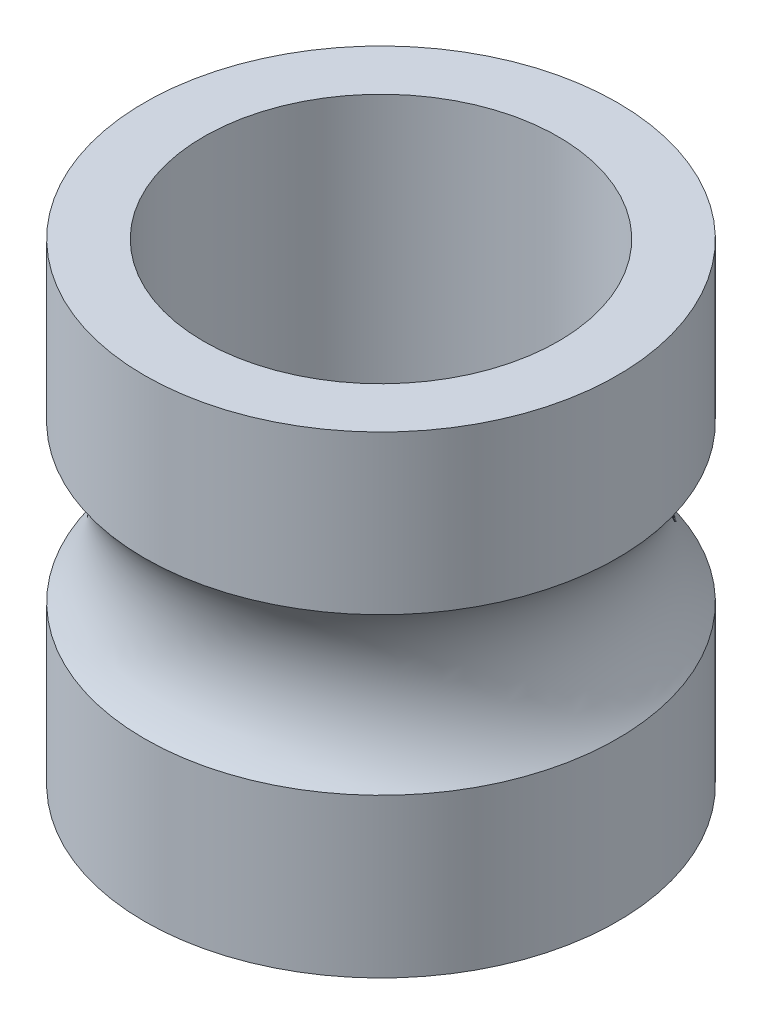
SolidWorks part; units mm, degrees
material "Chrome Stainless Steel"
ref_plane "Front Plane" through (0, 0, 0) normal (0, 0, 1) x (1, 0, 0)
ref_plane "Top Plane" through (0, 0, 0) normal (0, 1, 0) x (1, 0, 0)
ref_plane "Right Plane" through (0, 0, 0) normal (1, 0, 0) x (0, 0, -1)
sketch "DiaProfileS" plane through (0, 0, 0) normal (0, 1, 0) x (1, 0, 0)
  circle A0 centre (0, 0) radius 1.5
  circle A1 centre (0, 0) radius 2
  dimension "InnerDia" = 3
  dimension "Thickness" = 0.5
extrude "DiaProfile" add sketch "DiaProfileS" along normal mid plane 4
sketch "BearingPathProfileS" plane through (0, 0, 0) normal (0, 0, 1) x (1, 0, 0)
  line L0 (0, 0) -> (2.75, 0) construction
  line L3 (0, 2) -> (0, -2) construction
  circle A0 centre (2.75, 0) radius 1
  dimension "BallDia" = 2
  dimension "YDim" = 0.75
  dimension "RefRadius" = 2.75
revolve "BearingPathProfile" cut sketch "BearingPathProfileS" angle 360 about axis through (0, 2, 0) along (0, -1, 0)
